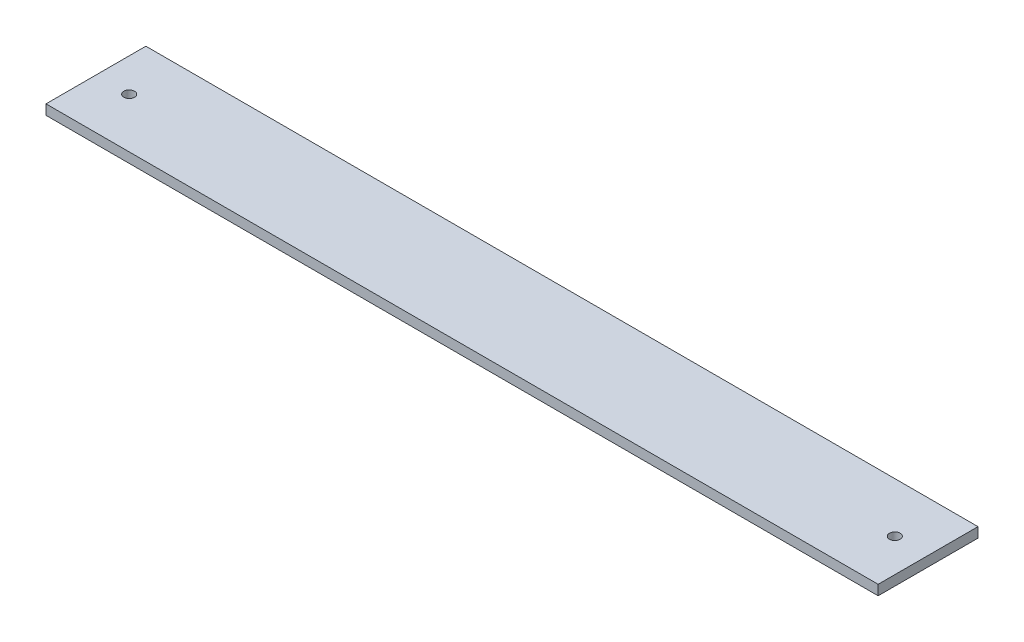
SolidWorks part; units mm, degrees
ref_plane "Front Plane" through (0, 0, 0) normal (0, 0, 1) x (1, 0, 0)
ref_plane "Top Plane" through (0, 0, 0) normal (0, 1, 0) x (1, 0, 0)
ref_plane "Right Plane" through (0, 0, 0) normal (1, 0, 0) x (0, 0, -1)
sketch "Sketch1" plane through (0, 0, 0) normal (0, 1, 0) x (1, 0, 0)
  line L1 (-125, 15) -> (125, 15)
  line L2 (-125, 15) -> (-125, -15)
  line L3 (-125, -15) -> (125, -15)
  line L4 (125, 15) -> (125, -15)
  line L5 (0, -15) -> (0, 15) construction
  line L6 (-125, 0) -> (125, 0) construction
  line L7 (-125, -15) -> (-115, -15) construction
  line L8 (-125, -15) -> (-125, 0) construction
  line L9 (-125, 0) -> (-115, 0) construction
  line L10 (-115, -15) -> (-115, 0) construction
  line L11 (-120, 0) -> (-120, -15) construction
  line L12 (-125, -7.5) -> (-115, -7.5) construction
  circle A0 centre (-115, 0) radius 1.6
  circle A1 centre (115, 0) radius 1.6
  point P0 (0, 0)
  point P141 (-120, -7.5)
  dimension "D5" = 3.2
  dimension "D1" = 30
  dimension "D2" = 250
  dimension "D3" = 15
  dimension "D4" = 10
extrude "Boss-Extrude1" add sketch "Sketch1" along normal blind 3
